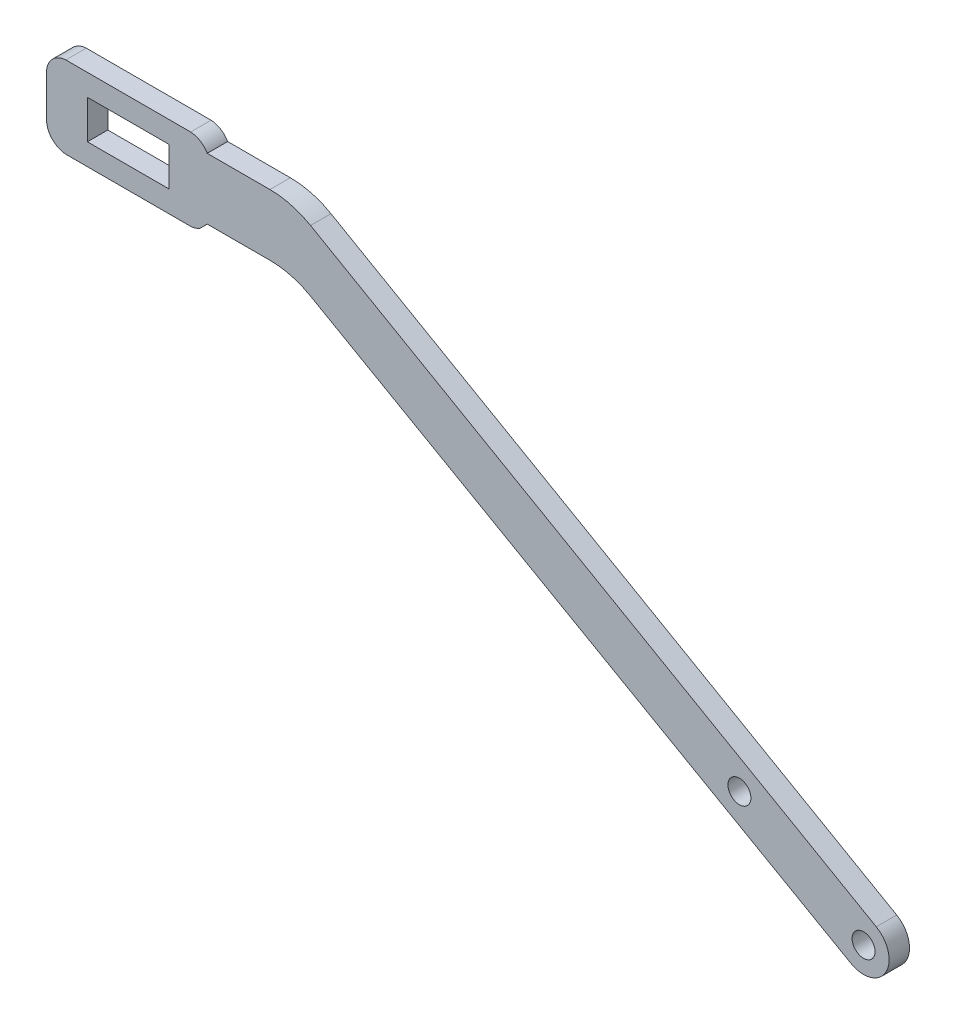
SolidWorks part; units mm, degrees
ref_plane "Front Plane" through (0, 0, 0) normal (0, 0, 1) x (1, 0, 0)
ref_plane "Top Plane" through (0, 0, 0) normal (0, 1, 0) x (1, 0, 0)
ref_plane "Right Plane" through (0, 0, 0) normal (1, 0, 0) x (0, 0, -1)
sketch "Sketch1" plane through (0, 0, 0) normal (0, 0, 1) x (1, 0, 0)
  line L0 (-30.3606, 18.0569) -> (-43.0606, 18.0569) construction
  line L1 (-25.5956, 12.1279) -> (-24.4317, 13.2968)
  line L2 (-27.0078, 24.4069) -> (-46.4134, 24.4069)
  line L3 (6.1174, 3.3779) -> (12.4118, -0.2055)
  line L4 (-30.3606, 15.0597) -> (-43.0606, 15.0597)
  line L5 (-30.3606, 15.0597) -> (-30.3606, 21.0541)
  line L6 (-30.3606, 21.0541) -> (-43.0606, 21.0541)
  line L7 (-43.0606, 15.0597) -> (-43.0606, 21.0541)
  line L8 (-36.7106, 21.0541) -> (-36.7106, 15.0597) construction
  line L9 (-30.3606, 18.0569) -> (-43.0606, 18.0569) construction
  line L10 (-27.0078, 11.7069) -> (-46.4134, 11.7069)
  line L11 (-49.4156, 14.8819) -> (-49.4156, 21.2319)
  line L12 (-24.0106, 18.0569) -> (-8.063, 18.0569) construction
  line L13 (-46.4134, 11.7069) -> (-46.4134, 24.4069) construction
  line L14 (-27.0078, 11.7069) -> (-27.0078, 24.4069) construction
  line L15 (-11.3106, 18.0569) -> (77.5894, -32.7431) construction
  line L16 (-11.3063, 13.2968) -> (-24.4317, 13.2968)
  line L17 (-11.3063, 22.8218) -> (-24.4317, 22.8218)
  line L18 (-11.3063, 22.8218) -> (79.5641, -29.3005)
  line L19 (-11.3063, 13.2968) -> (6.1174, 3.3779)
  line L20 (12.4118, -0.2055) -> (75.6259, -36.1922)
  arc A0 (-46.4134, 24.4069) -> (-49.4156, 21.2319) centre (-46.2356, 21.2319) ccw
  arc A1 (-46.4134, 11.7069) -> (-49.4156, 14.8819) centre (-46.2356, 14.8819) cw
  arc A2 (-27.0078, 11.7069) -> (-25.5956, 12.1279) centre (-27.1856, 14.8819) ccw
  arc A3 (-27.0078, 24.4069) -> (-24.4317, 22.8218) centre (-27.1856, 21.2319) cw
  circle A4 centre (77.5894, -32.7431) radius 1.7859
  arc A5 (75.6259, -36.1922) -> (79.5641, -29.3005) centre (77.5894, -32.7431) ccw
  point P2 (-36.7106, 18.0569)
  point P7 (-36.7106, 18.0569)
  point P23 (-11.3106, 18.0569)
  dimension "D2" = 12.7
  dimension "D9" = 3.5719
  dimension "D10" = 7.9375
  dimension "D1" = 12.7
  dimension "D3" = 12.7
  dimension "D4" = 5.9944
  dimension "D6" = 9.525
  dimension "D7" = 50.8
  dimension "D8" = 88.9
extrude "Boss-Extrude1" add sketch "Sketch1" along normal blind 3.175
fillet "Fillet2" radius 12.7 2 edges at (-11.3063, 22.8218, 1.5875) (-11.3063, 13.2968, 1.5875)
hole_wizard "9/64 (0.14063) Diameter Hole1" positions "Sketch3" profile "Sketch2" hole size "9/64" standard "ANSI Inch" end condition through all
sketch "Sketch3" plane through (0, 0, 3.175) normal (0, 0, 1) x (1, 0, 0)
  line L0 (77.5894, -32.7431) -> (81.0352, -34.7122) construction
  line L1 (81.0352, -34.7122) -> (47.5644, -15.5858) construction
  arc A0 (75.6259, -36.1922) -> (79.5641, -29.3005) centre (77.5894, -32.7431) ccw construction
  point P11 (58.2927, -21.7164)
  dimension "D1" = 22.225
sketch "Sketch2" plane through (58.2927, -21.7164, 3.175) normal (1, 0, 0) x (0, -1, 0)
  line L0 (0, 0) -> (0, 3.175)
  line L1 (0, 3.175) -> (1.786, 3.175)
  line L2 (1.786, 3.175) -> (1.786, 0)
  line L5 (1.786, 0) -> (0, 0)
  line L11 (0, -6.35) -> (0, 107.95) construction
  dimension "Thru Hole Dia." = 3.572
  dimension "Thru Hole Depth" = 3.175
